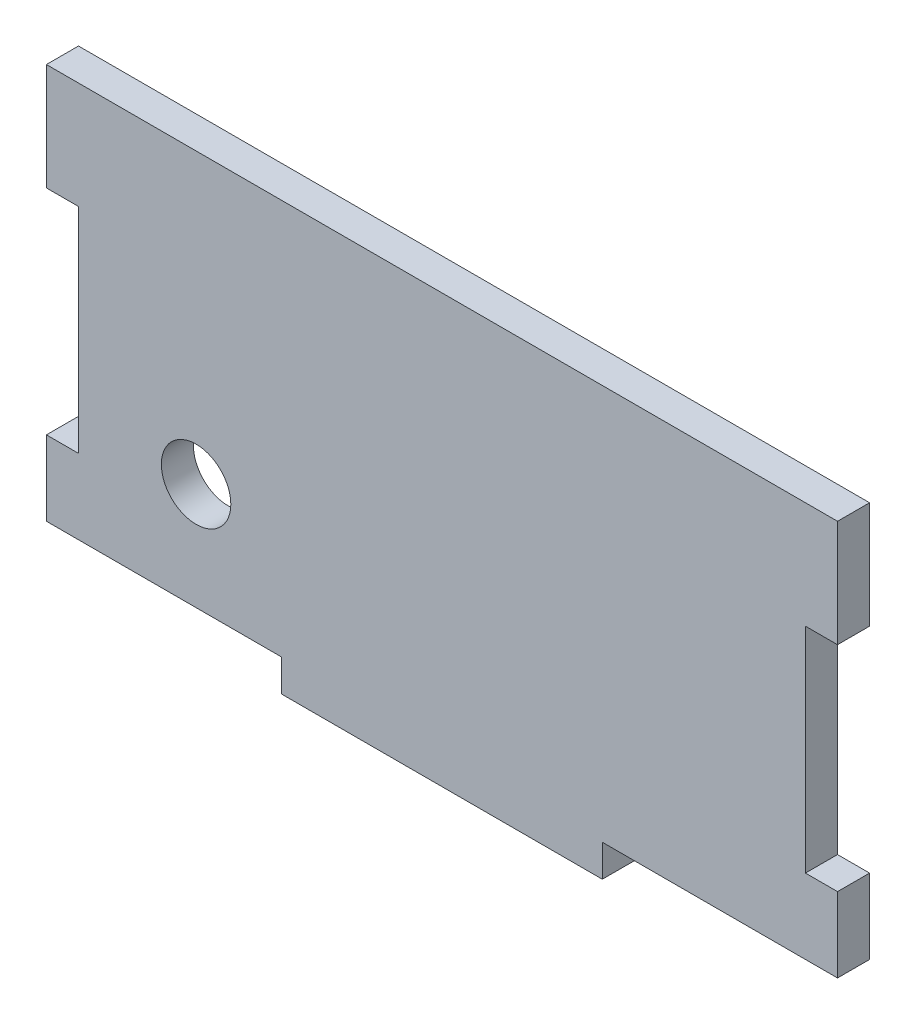
SolidWorks part; units mm, degrees
ref_plane "Plano frontal" through (0, 0, 0) normal (0, 0, 1) x (1, 0, 0)
ref_plane "Plano superior" through (0, 0, 0) normal (0, 1, 0) x (1, 0, 0)
ref_plane "Plano direito" through (0, 0, 0) normal (1, 0, 0) x (0, 0, -1)
sketch "Esboço1" plane through (0, 0, 0) normal (0, 0, 1) x (1, 0, 0)
  line L1 (-37, -20) -> (37, -20)
  line L2 (-37, -20) -> (-37, 20)
  line L3 (-37, 20) -> (37, 20)
  line L4 (37, -20) -> (37, 20)
  line L5 (-37, -20) -> (37, 20) construction
  line L6 (-37, 20) -> (37, -20) construction
  point P0 (0, 0)
  dimension "D1" = 74
  dimension "D2" = 40
extrude "Ressalto-extrusão1" add sketch "Esboço1" along normal blind 3
sketch "Esboço2" plane through (0, 0, 3) normal (0, 0, 1) x (1, 0, 0)
  line L0 (-37, -20) -> (37, -20) construction
  line L1 (-15, -20) -> (15, -20) construction
  line L2 (-15, -20) -> (-15, -17) construction
  line L3 (-15, -17) -> (15, -17) construction
  line L4 (15, -20) -> (15, -17) construction
  line L5 (-37, 20) -> (-37, -20) construction
  line L6 (-15, -20) -> (-37, -20)
  line L7 (-15, -20) -> (-15, -17)
  line L8 (-15, -17) -> (-37, -17)
  line L9 (-37, -20) -> (-37, -17)
  line L10 (0, 29.2787) -> (0, -21.4217) construction
  line L11 (15, -17) -> (37, -17)
  line L12 (15, -17) -> (15, -20)
  line L13 (15, -20) -> (37, -20)
  line L14 (37, -17) -> (37, -20)
  line L15 (-37, 10) -> (-34, 10)
  line L16 (-37, 10) -> (-37, -10)
  line L17 (-37, -10) -> (-34, -10)
  line L18 (-34, 10) -> (-34, -10)
  line L19 (34, 10) -> (34, -10)
  line L20 (37, -10) -> (34, -10)
  line L21 (37, 10) -> (37, -10)
  line L22 (37, 10) -> (34, 10)
  point P6 (0, -17)
  point P16 (-34, 0)
  dimension "D1" = 30
  dimension "D2" = 3
  dimension "D3" = 20
extrude "Corte-extrusão1" cut sketch "Esboço2" against normal blind 3
sketch "Esboço3" plane through (0, 0, 3) normal (0, 0, 1) x (1, 0, 0)
  line L0 (-15, -17) -> (-37, -17) construction
  line L1 (-34, -10) -> (-34, 10) construction
  circle A0 centre (-23, -7) radius 3.25
  dimension "D1" = 10
  dimension "D2" = 6.5
  dimension "D3" = 11
extrude "Corte-extrusão2" cut sketch "Esboço3" against normal blind 10
